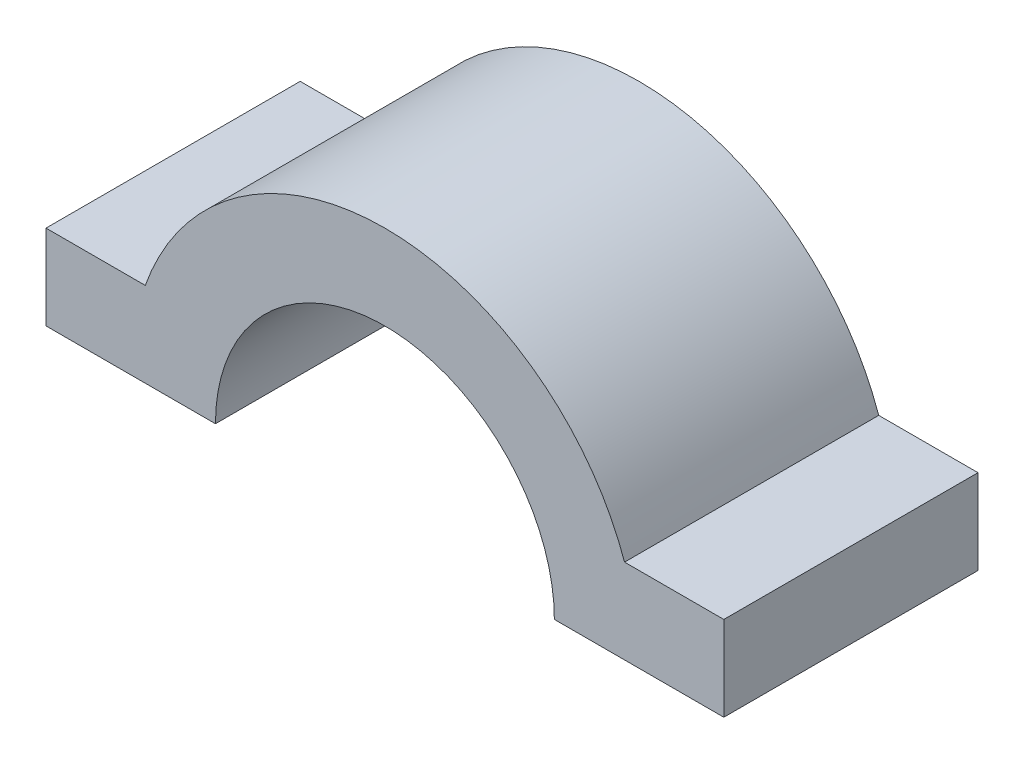
SolidWorks part; units mm, degrees
ref_plane "Alzado" through (0, 0, 0) normal (0, 0, 1) x (1, 0, 0)
ref_plane "Planta" through (0, 0, 0) normal (0, 1, 0) x (1, 0, 0)
ref_plane "Vista lateral" through (0, 0, 0) normal (1, 0, 0) x (0, 0, -1)
sketch "Croquis1" plane through (0, 0, 0) normal (0, 1, 0) x (1, 0, 0)
  line L1 (0, 0) -> (40, 0)
  line L2 (0, 0) -> (0, -15)
  line L3 (0, -15) -> (40, -15)
  line L4 (40, 0) -> (40, -15)
  dimension "D1" = 40
  dimension "D2" = 15
extrude "Saliente-Extruir1" add sketch "Croquis1" along normal blind 15
sketch "Croquis2" plane through (0, 0, 15) normal (0, 0, 1) x (1, 0, 0)
  line L0 (20, 15) -> (20, 0) construction
  line L1 (0, 15) -> (10, 15)
  line L2 (0, 15) -> (0, 5)
  line L3 (0, 5) -> (10, 5)
  line L4 (10, 15) -> (10, 5)
  line L5 (0, 15) -> (40, 15) construction
  line L6 (0, 0) -> (40, 0) construction
  line L7 (40, 5) -> (30, 5)
  line L8 (30, 15) -> (30, 5)
  line L9 (40, 15) -> (30, 15)
  line L10 (40, 15) -> (40, 5)
  dimension "D1" = 10
  dimension "D2" = 10
extrude "Cortar-Extruir2" cut sketch "Croquis2" against normal blind 15
sketch "Croquis5" plane through (0, 0, 15) normal (0, 0, 1) x (1, 0, 0)
  line L9 (0, 0) -> (40, 0) construction
  line L13 (30, 5) -> (30, 0)
  line L19 (10, 0) -> (30, 0)
  circle A0 centre (20, 0) radius 10
  line M13 (0, 0) -> (40, 0)
extrude "Cortar-Extruir3" cut sketch "Croquis5" against normal blind 15 contours A0 M13
sketch "Croquis6" plane through (0, 0, 15) normal (0, 0, 1) x (1, 0, 0)
  line L0 (10, 0) -> (30, 0) construction
  line L1 (10, 15) -> (10, 11.1803)
  line L2 (10, 5) -> (10, 15) construction
  line L3 (10, 15) -> (20, 15)
  line L4 (20, 15) -> (30, 15)
  line L5 (30, 15) -> (30, 11.1803)
  line L6 (30, 15) -> (30, 5) construction
  circle A0 centre (20, 0) radius 15
  line M7 (30, 5) -> (30, 15)
  line M8 (30, 15) -> (10, 15)
  line M9 (10, 15) -> (10, 5)
  dimension "D1" = 30
extrude "Cortar-Extruir4" cut sketch "Croquis6" against normal blind 15 contours A0 M8 M9 | A0 M7 M8
sketch "Croquis7" plane through (0, 0, 15) normal (0, 0, 1) x (1, 0, 0)
  line L0 (10, 0) -> (30, 0) construction
  line L1 (5, 0) -> (35, 0)
  circle A0 centre (20, 0) radius 15
  line M2 (30, 5) -> (30, 11.1803)
  line M4 (10, 11.1803) -> (10, 5)
  line M5 (10, 5) -> (0, 5)
  line M11 (40, 5) -> (30, 5)
extrude "Saliente-Extruir2" add sketch "Croquis7" against normal blind 15 contours A0 M4 M5 | A0 M11 M2
